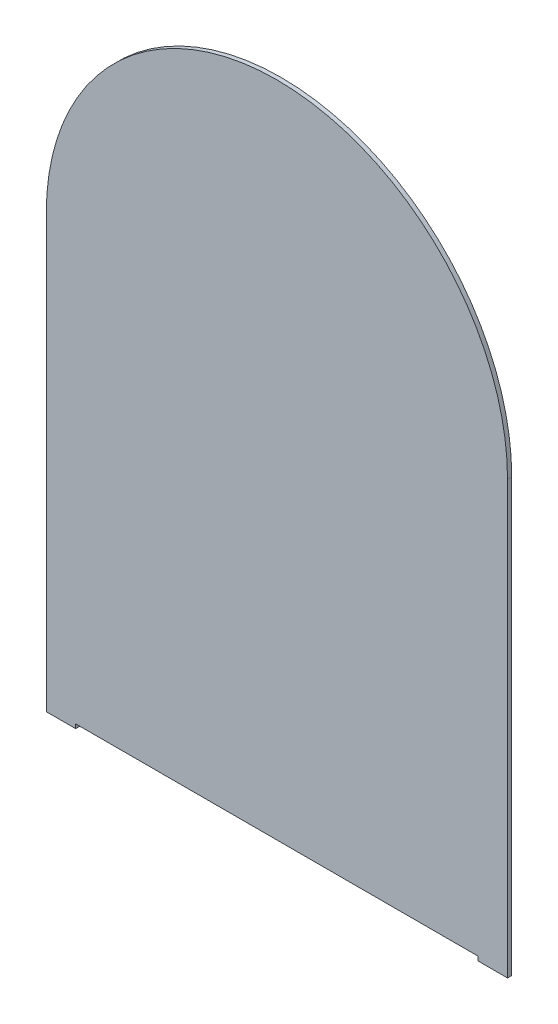
SolidWorks part; units mm, degrees
ref_plane "Front" through (0, 0, 0) normal (0, 0, 1) x (1, 0, 0)
ref_plane "Top" through (0, 0, 0) normal (0, 1, 0) x (1, 0, 0)
ref_plane "Right" through (0, 0, 0) normal (1, 0, 0) x (0, 0, -1)
sketch "Sketch1" plane through (0, 0, 0) normal (0, 0, 1) x (1, 0, 0)
  line L2 (0, 0) -> (0, -327.025)
  line L3 (0, -327.025) -> (349.25, -327.025)
  line L4 (349.25, 0) -> (349.25, -327.025)
  arc A0 (0, 0) -> (349.25, 0) centre (174.625, 0) cw
  dimension "D1" = 327.025
  dimension "D2" = 349.25
extrude "Boss-Extrude1" add sketch "Sketch1" along normal blind 3.175
sketch "Sketch2" plane through (0, 0, 3.175) normal (0, 0, 1) x (1, 0, 0)
  line L0 (0, -327.025) -> (349.25, -327.025) construction
  line L1 (22.225, -323.85) -> (327.025, -323.85)
  line L2 (22.225, -323.85) -> (22.225, -327.025)
  line L3 (22.225, -327.025) -> (327.025, -327.025)
  line L4 (327.025, -323.85) -> (327.025, -327.025)
  point P6 (174.625, -327.025)
  dimension "D1" = 304.8
  dimension "D2" = 3.175
extrude "Cut-Extrude1" cut sketch "Sketch2" against normal blind 3.175
